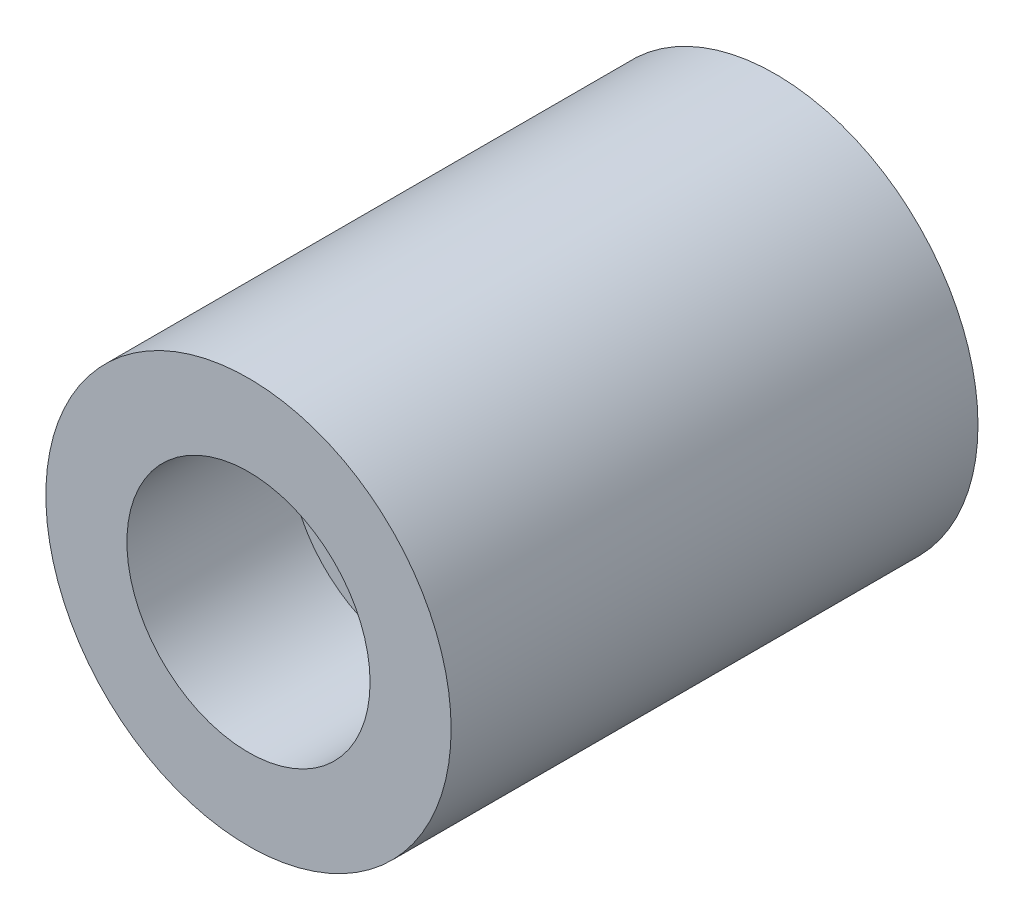
SolidWorks part; units mm, degrees
ref_plane "Front Plane" through (0, 0, 0) normal (0, 0, 1) x (1, 0, 0)
ref_plane "Top Plane" through (0, 0, 0) normal (0, 1, 0) x (1, 0, 0)
ref_plane "Right Plane" through (0, 0, 0) normal (1, 0, 0) x (0, 0, -1)
sketch "Sketch1" plane through (0, 0, 0) normal (0, 0, 1) x (1, 0, 0)
  circle A0 centre (0, 0) radius 50
  dimension "D1" = 100
extrude "Boss-Extrude1" add sketch "Sketch1" along normal blind 130 contours A0
sketch "Sketch2" plane through (0, 0, 130) normal (0, 0, 1) x (1, 0, 0)
  circle A0 centre (0, 0) radius 30
  dimension "D1" = 60
extrude "Cut-Extrude1" cut sketch "Sketch2" against normal blind 40
sketch "Sketch3" plane through (0, 0, 90) normal (0, 0, 1) x (1, 0, 0)
  circle A0 centre (0, 0) radius 10
  dimension "D1" = 20
extrude "Cut-Extrude2" cut sketch "Sketch3" against normal blind 80
